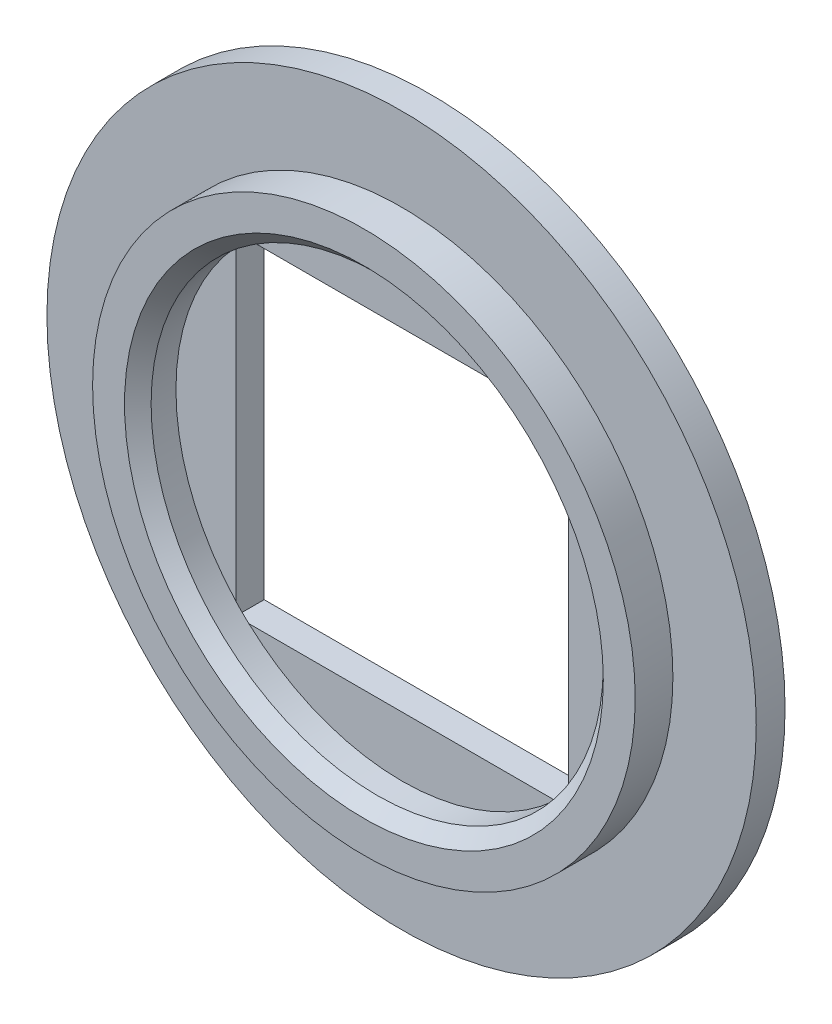
SolidWorks part; units mm, degrees
ref_plane "前视基准面" through (0, 0, 0) normal (0, 0, 1) x (1, 0, 0)
ref_plane "上视基准面" through (0, 0, 0) normal (0, 1, 0) x (1, 0, 0)
ref_plane "右视基准面" through (0, 0, 0) normal (1, 0, 0) x (0, 0, -1)
sketch "草图1" plane through (0, 0, 0) normal (0, 0, 1) x (1, 0, 0)
  circle A0 centre (0, 0) radius 8
extrude "凸台-拉伸1" add sketch "草图1" along normal blind 0.65
sketch "草图2" plane through (0, 0, 0) normal (0, 0, 1) x (1, 0, 0)
  circle A0 centre (0, 0) radius 6.12
  circle A1 centre (0, 0) radius 5.1
extrude "凸台-拉伸2" add sketch "草图2" along normal blind 0.85 from surface at 0.65 starting at face at (8, 0, 0.65)
sketch "草图3" plane through (0, 0, 0) normal (0, 0, 1) x (1, 0, 0)
  circle A0 centre (0, 0) radius 5.1
extrude "切除-拉伸1" cut sketch "草图3" against normal blind 0.01 from surface at 0.65 starting at face at (6.12, 0, 0.65)
sketch "草图4" plane through (0, 0, 0) normal (0, 0, 1) x (1, 0, 0)
  line L0 (3.75, 3.75) -> (3.75, -3.75)
  line L2 (-3.75, 0) -> (-3.75, 3.75)
  line L3 (-3.75, 3.75) -> (3.75, 3.75)
  line L13 (3.75, -3.75) -> (-3.75, -3.75)
  line L14 (-3.75, 0) -> (-3.75, -3.75)
extrude "切除-拉伸2" cut sketch "草图4" along normal up to surface (0.64 mm away) up to face at (5.1, 0, 0.64)
chamfer "倒角1" distance 0.3 angle 45 1 edges at (5.1, 0, 1.5)
